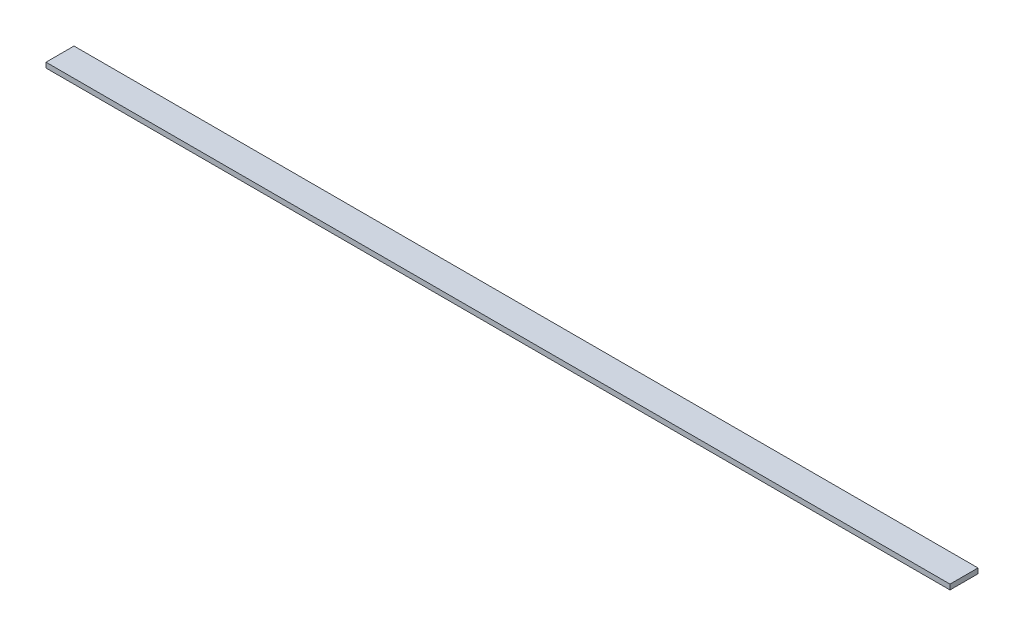
SolidWorks part; units mm, degrees
ref_plane "Front Plane" through (0, 0, 0) normal (0, 0, 1) x (1, 0, 0)
ref_plane "Top Plane" through (0, 0, 0) normal (0, 1, 0) x (1, 0, 0)
ref_plane "Right Plane" through (0, 0, 0) normal (1, 0, 0) x (0, 0, -1)
sketch "Sketch1" plane through (0, 0, 0) normal (0, 1, 0) x (1, 0, 0)
  line L1 (0, 0) -> (4508.5, 0)
  line L2 (0, 0) -> (0, 139.7)
  line L3 (0, 139.7) -> (4508.5, 139.7)
  line L4 (4508.5, 0) -> (4508.5, 139.7)
  dimension "D1" = 139.7
  dimension "D2" = 4508.5
extrude "Boss-Extrude1" add sketch "Sketch1" along normal blind 25.4
